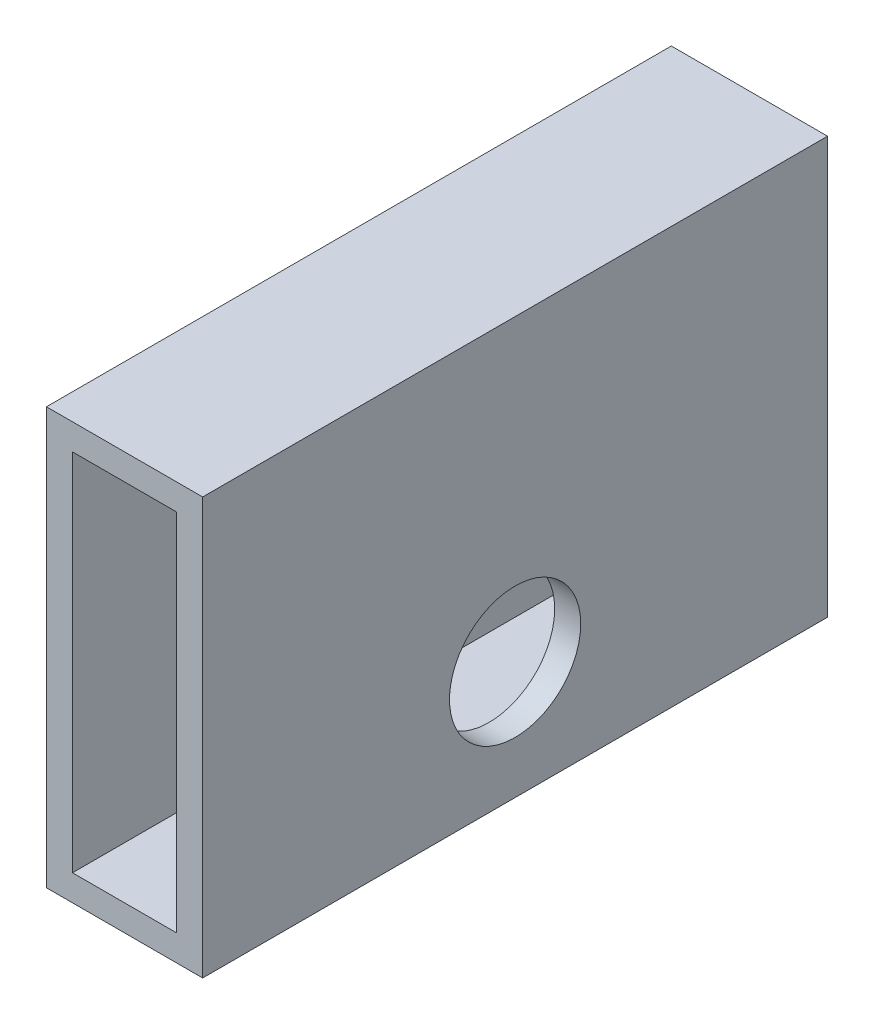
SolidWorks part; units mm, degrees
ref_plane "Front Plane" through (0, 0, 0) normal (0, 0, 1) x (1, 0, 0)
ref_plane "Top Plane" through (0, 0, 0) normal (0, 1, 0) x (1, 0, 0)
ref_plane "Right Plane" through (0, 0, 0) normal (1, 0, 0) x (0, 0, -1)
sketch "Sketch1" plane through (0, 0, 0) normal (0, 0, 1) x (1, 0, 0)
  line L1 (-9.525, -25.4) -> (9.525, -25.4)
  line L2 (-9.525, -25.4) -> (-9.525, 25.4)
  line L3 (-9.525, 25.4) -> (9.525, 25.4)
  line L4 (9.525, -25.4) -> (9.525, 25.4)
  line L5 (-9.525, -25.4) -> (9.525, 25.4) construction
  line L6 (-9.525, 25.4) -> (9.525, -25.4) construction
  point P0 (0, 0)
  dimension "D1" = 19.05
  dimension "D2" = 50.8
extrude "Boss-Extrude1" add sketch "Sketch1" against normal blind 76.2
sketch "Sketch2" plane through (0, 0, 0) normal (0, 0, 1) x (1, 0, 0)
  line L1 (-6.35, -22.225) -> (6.35, -22.225)
  line L2 (-6.35, -22.225) -> (-6.35, 22.225)
  line L3 (-6.35, 22.225) -> (6.35, 22.225)
  line L4 (6.35, -22.225) -> (6.35, 22.225)
  line L5 (-6.35, -22.225) -> (6.35, 22.225) construction
  line L6 (-6.35, 22.225) -> (6.35, -22.225) construction
  point P0 (0, 0)
  dimension "D1" = 12.7
  dimension "D2" = 44.45
extrude "Cut-Extrude1" cut sketch "Sketch2" against normal up to next
sketch "Sketch4" plane through (9.525, 0, 0) normal (1, 0, 0) x (0, 0, -1)
  line L0 (38.1, 25.4) -> (38.1, -25.4) construction
  line L1 (76.2, 25.4) -> (0, 25.4) construction
  line L2 (76.2, -25.4) -> (0, -25.4) construction
  circle A0 centre (38.1, -11.049) radius 8.001
  dimension "D1" = 16.002
  dimension "D2" = 14.351
extrude "Cut-Extrude2" cut sketch "Sketch4" against normal through all
equation "\"D2@Sketch4\"=(\"D1@Sketch4\"/2)+0.25"
